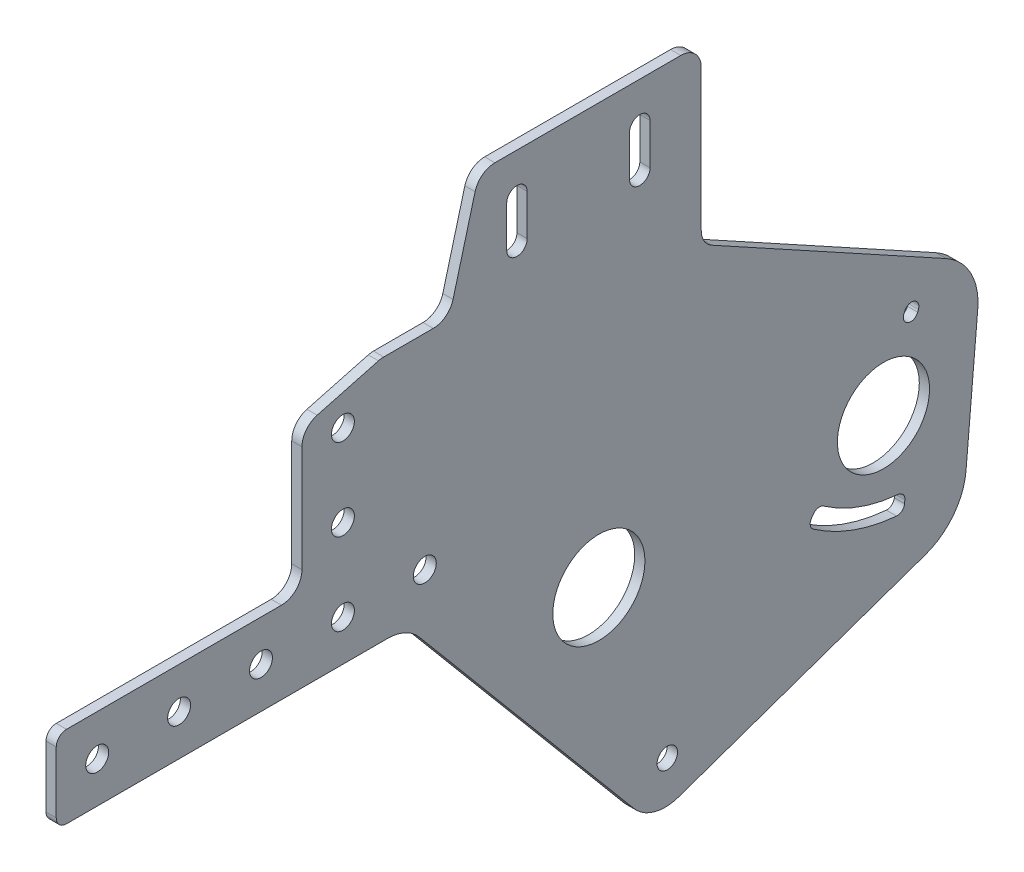
SolidWorks part; units mm, degrees
ref_plane "Front Plane" through (0, 0, 0) normal (0, 0, 1) x (1, 0, 0)
ref_plane "Top Plane" through (0, 0, 0) normal (0, 1, 0) x (1, 0, 0)
ref_plane "Right Plane" through (0, 0, 0) normal (1, 0, 0) x (0, 0, -1)
sketch "Sketch2" plane through (0, 0, 0) normal (1, 0, 0) x (0, 0, -1)
  line L0 (-165.1, 19.05) -> (-65.426, 19.05)
  line L1 (24.7789, -68.6236) -> (101.1789, -41.8834)
  line L2 (-168.275, 22.225) -> (-168.275, 41.275)
  line L3 (-165.1, 44.45) -> (-98.425, 44.45)
  line L4 (-38.3848, 125.4685) -> (-45.2207, 99.9565)
  line L5 (41.6129, 175.1877) -> (218.62, -77.6046) construction
  line L6 (15.0515, 157.8062) -> (118.3631, 25.535) construction
  line L7 (53.6439, -14.125) -> (-17.3081, 137.9762) construction
  line L8 (-4.6354, 18.5275) -> (78.6163, 39.3564) construction
  line L9 (80.5683, -35.188) -> (-3.6594, -18.7447) construction
  line L10 (96.725, 25.2801) -> (96.9473, 25.8909) construction
  line L11 (55, 0) -> (-55, 0) construction
  line L12 (10.8546, -64.8) -> (-55.6972, 14.5134)
  line L13 (0, 95.25) -> (255.6229, 95.25) construction
  line L14 (0, 50.8) -> (255.6229, 50.8) construction
  line L15 (117.5095, 16.1148) -> (113.8632, -25.5632)
  line L16 (31.75, 123.825) -> (31.75, 79.9566)
  line L17 (94.5769, 26.062) -> (94.7992, 26.6728)
  line L18 (98.8732, 24.4983) -> (99.0955, 25.1091)
  line L19 (68.3924, -14.8897) -> (67.8097, -15.722) construction
  line L21 (66.5198, -13.5785) -> (65.9371, -14.4108)
  line L22 (92.6084, -23.7036) -> (92.5198, -24.7158) construction
  line L23 (94.8857, -23.9029) -> (94.7971, -24.915)
  line L26 (96.9473, 25.8909) -> (68.3924, -14.8897) construction
  line L27 (96.9473, 25.8909) -> (92.6084, -23.7036) construction
  line L28 (88.26, 2.0227) -> (96.9473, 25.8909) construction
  line L29 (-92.075, 50.8) -> (-92.075, 83.8035)
  line L30 (-66.7045, 95.25) -> (-51.3544, 95.25)
  line L31 (-68.348, 95.0336) -> (-87.3685, 89.9371)
  line L32 (0, 0) -> (87.8872, 2.3014) construction
  line L33 (0, 146.05) -> (88.26, 2.0227) construction
  line L34 (0, 55) -> (0, -55) construction
  line L35 (35.0424, 74.3912) -> (107.7047, 34.4713)
  line L36 (-32.2512, 130.175) -> (25.4, 130.175)
  line L37 (-25.4, 117.475) -> (-25.4, 104.775) construction
  line L38 (-22.225, 117.475) -> (-22.225, 104.775)
  line L39 (-28.575, 117.475) -> (-28.575, 104.775)
  line L40 (12.7, 117.475) -> (12.7, 104.775) construction
  line L41 (15.875, 117.475) -> (15.875, 104.775)
  line L42 (9.525, 117.475) -> (9.525, 104.775)
  line L43 (-53.975, 31.75) -> (6.3144, -68.5885) construction
  line L44 (-32.203, 44.832) -> (28.0865, -55.5065) construction
  line L45 (4.8939, -66.2242) -> (21.2229, -56.4127) construction
  circle A0 centre (0, 146.05) radius 14.2875 construction
  circle A1 centre (0, 0) radius 14.2875
  circle A2 centre (0, 146.05) radius 50.8 construction
  circle A3 centre (0, 0) radius 50.8 construction
  circle A5 centre (-53.975, 31.75) radius 3.556
  circle A6 centre (-79.375, 31.75) radius 3.556
  circle A7 centre (-104.775, 31.75) radius 3.556
  circle A8 centre (-130.175, 31.75) radius 3.556
  circle A9 centre (-155.575, 31.75) radius 3.556
  arc A10 (31.75, 146.05) -> (-30.6681, 154.2675) centre (0, 146.05) ccw construction
  arc A11 (-168.275, 41.275) -> (-165.1, 44.45) centre (-165.1, 41.275) cw
  arc A12 (-165.1, 19.05) -> (-168.275, 22.225) centre (-165.1, 22.225) cw
  arc A14 (-55.6972, 14.5134) -> (-65.426, 19.05) centre (-65.426, 6.35) ccw
  arc A15 (-4.6354, 18.5275) -> (-3.6594, -18.7447) centre (0, 0) ccw construction
  arc A16 (15.0515, 157.8062) -> (-17.3081, 137.9762) centre (0, 146.05) ccw construction
  arc A17 (53.6439, -14.125) -> (118.3631, 25.535) centre (88.26, 2.0227) ccw construction
  arc A18 (80.5683, -35.188) -> (78.6163, 39.3564) centre (87.8872, 2.3014) ccw construction
  circle A19 centre (87.8872, 2.3014) radius 32 construction
  circle A20 centre (88.26, 2.0227) radius 32 construction
  circle A21 centre (88.26, 2.0227) radius 24.75 construction
  circle A24 centre (87.8872, 2.3014) radius 24.75 construction
  arc A30 (117.5095, 16.1148) -> (107.7047, 34.4713) centre (98.532, 17.7751) ccw
  arc A31 (101.1789, -41.8834) -> (113.8632, -25.5632) centre (94.8857, -23.9029) ccw
  circle A32 centre (88.26, 2.0227) radius 14.2875
  circle A33 centre (87.8872, 2.3014) radius 14.2875 construction
  arc A34 (94.5769, 26.062) -> (98.8732, 24.4983) centre (96.725, 25.2801) ccw
  arc A35 (99.0955, 25.1091) -> (94.7992, 26.6728) centre (96.9473, 25.8909) ccw
  arc A37 (65.9371, -14.4108) -> (66.4985, -17.5946) centre (67.8097, -15.722) ccw
  arc A38 (94.8857, -23.9029) -> (92.8076, -21.4263) centre (92.6084, -23.7036) ccw
  arc A39 (92.3206, -26.9931) -> (94.7971, -24.915) centre (92.5198, -24.7158) ccw
  arc A40 (69.7036, -13.0172) -> (92.8076, -21.4263) centre (96.9473, 25.8909) ccw
  arc A41 (66.4985, -17.5946) -> (92.3206, -26.9931) centre (96.9473, 25.8909) ccw
  arc A42 (69.7036, -13.0172) -> (66.5198, -13.5785) centre (68.3924, -14.8897) ccw
  circle A43 centre (-79.375, 57.15) radius 3.556
  circle A44 centre (-79.375, 82.55) radius 3.556
  arc A45 (-51.3544, 95.25) -> (-45.2207, 99.9565) centre (-51.3544, 101.6) ccw
  arc A46 (-92.075, 50.8) -> (-98.425, 44.45) centre (-98.425, 50.8) cw
  arc A48 (-87.3685, 89.9371) -> (-92.075, 83.8035) centre (-85.725, 83.8035) ccw
  arc A49 (-68.348, 95.0336) -> (-66.7045, 95.25) centre (-66.7045, 88.9) cw
  arc A50 (35.0424, 74.3912) -> (31.75, 79.9566) centre (38.1, 79.9566) cw
  arc A53 (25.4, 130.175) -> (31.75, 123.825) centre (25.4, 123.825) cw
  arc A54 (-32.2512, 130.175) -> (-38.3848, 125.4685) centre (-32.2512, 123.825) ccw
  arc A55 (-22.225, 117.475) -> (-28.575, 117.475) centre (-25.4, 117.475) ccw
  arc A56 (-28.575, 104.775) -> (-22.225, 104.775) centre (-25.4, 104.775) ccw
  arc A57 (15.875, 117.475) -> (9.525, 117.475) centre (12.7, 117.475) ccw
  arc A58 (9.525, 104.775) -> (15.875, 104.775) centre (12.7, 104.775) ccw
  circle A59 centre (21.2229, -56.4127) radius 3.175
  arc A60 (10.8546, -64.8) -> (24.7789, -68.6236) centre (20.5834, -56.6366) ccw
  point P50 (96.8362, 25.5855)
  point P76 (-92.075, 88.676)
  point P79 (102.7469, -16.3909)
  point P97 (-67.5405, 95.25)
  point P104 (-25.4, 111.125)
  point P113 (31.75, 76.2)
  point P124 (12.7, 111.125)
  dimension "D1" = 28.575
  dimension "D2" = 101.6
  dimension "D3" = 44.45
  dimension "D4" = 19.05
  dimension "D6" = 19.05
  dimension "D8" = 7.112
  dimension "D14" = 105
  dimension "D15" = 3.175
  dimension "D16" = 12.7
  dimension "D18" = 38.1972
  dimension "D19" = 76.3944
  dimension "D20" = 520
  dimension "D21" = 360
  dimension "D22" = 64
  dimension "D23" = 49.5
  dimension "D24" = 4.572
  dimension "D25" = 19.05
  dimension "D26" = 31.75
  dimension "D27" = 25.4
  dimension "D28" = 2.286
  dimension "D29" = 1.016
  dimension "D36" = 25.4
  dimension "D38" = 12.7
  dimension "D39" = 6.35
  dimension "D40" = 15
  dimension "D42" = 6.35
  dimension "D43" = 5.588
  dimension "D44" = 58.5
  dimension "D47" = 19.05
  dimension "D48" = 12.7
  dimension "D50" = 6.35
  dimension "D51" = 12.7
  dimension "D52" = 15.875
  dimension "D53" = 12.7
  dimension "D54" = 121
  dimension "D55" = 25.4
  dimension "D56" = 6.35
  dimension "D62" = 6.35
  dimension "D64" = 12.7
  dimension "D5" = 130
  dimension "D7" = 12.7
  dimension "D9" = 53.975
  dimension "D10" = 12.7
  dimension "D12" = 25.4
  dimension "D13" = 12.7
  dimension "D17" = 55
  dimension "D30" = 3
  dimension "D31" = 30
  dimension "D32" = 15
  dimension "D33" = 50.8
  dimension "D34" = 50.8
  dimension "D35" = 1.016
  dimension "D37" = 12.7
  dimension "D41" = 25.4
  dimension "D45" = 1.5
  dimension "D46" = 110
  dimension "D57" = 6.35
  dimension "D58" = 12.7
  dimension "D60" = 114.3
  dimension "D61" = 19.05
  dimension "D63" = 9.525
  dimension "D59" = 25.4
  dimension "D11" = 5
extrude "Boss-Extrude1" add sketch "Sketch2" along normal blind 3.175
